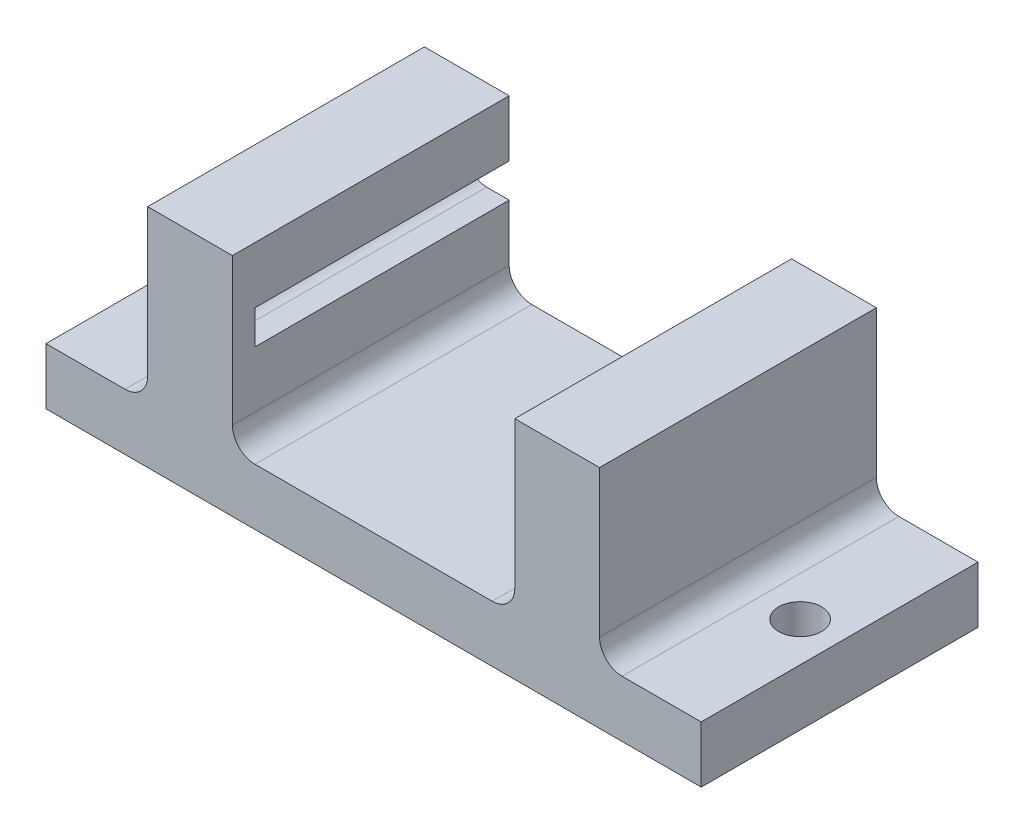
SolidWorks part; units mm, degrees
material "PVC Rigid"
ref_plane "Front Plane" through (0, 0, 0) normal (0, 0, 1) x (1, 0, 0)
ref_plane "Top Plane" through (0, 0, 0) normal (0, 1, 0) x (1, 0, 0)
ref_plane "Right Plane" through (0, 0, 0) normal (1, 0, 0) x (0, 0, -1)
sketch "Sketch2" plane through (0, 0, 0) normal (0, 0, 1) x (1, 0, 0)
  line L0 (13.335, -19.05) -> (0, -19.05)
  line L1 (0, -25.4) -> (36.83, -25.4)
  line L2 (36.83, -25.4) -> (36.83, -19.05)
  line L3 (25.4, 0) -> (15.875, 0)
  line L4 (15.875, 0) -> (15.875, -6.35)
  line L5 (0, -19.05) -> (0, -25.4)
  line L6 (15.875, -16.51) -> (15.875, -10.16)
  line L7 (25.4, -16.51) -> (25.4, 0)
  line L8 (36.83, -19.05) -> (27.94, -19.05)
  line L9 (15.875, -10.16) -> (18.415, -10.16)
  line L10 (15.875, -6.35) -> (18.415, -6.35)
  arc A0 (13.335, -19.05) -> (15.875, -16.51) centre (13.335, -16.51) ccw
  arc A1 (18.415, -10.16) -> (18.415, -6.35) centre (18.415, -8.255) ccw
  arc A2 (25.4, -16.51) -> (27.94, -19.05) centre (27.94, -16.51) ccw
  dimension "D3" = 2.54
  dimension "D5" = 1.905
  dimension "D9" = 2.54
  dimension "D1" = 25.4
  dimension "D2" = 6.35
  dimension "D4" = 15.875
  dimension "D6" = 25.4
  dimension "D7" = 6.35
  dimension "D8" = 6.35
  dimension "D10" = 8.89
  dimension "D11" = 2.54
extrude "Base" add sketch "Sketch2" along normal blind 28.575
sketch "Sketch5" plane through (0, 0, 28.575) normal (0, 0, 1) x (1, 0, 0)
  line L1 (0, -25.4) -> (36.83, -25.4)
  line L2 (0, -19.05) -> (0, -25.4) construction
  line L3 (13.335, -19.05) -> (0, -19.05) construction
  line L4 (36.83, -25.4) -> (36.83, -19.05) construction
  line L6 (36.83, -19.05) -> (27.94, -19.05) construction
  line L7 (25.4, -16.51) -> (25.4, 0) construction
  line L8 (36.83, -25.4) -> (36.83, -19.05)
  line L9 (36.83, -19.05) -> (27.94, -19.05)
  line L10 (25.4, -16.51) -> (25.4, 0)
  line L11 (15.875, -10.16) -> (15.875, -16.51) construction
  line L12 (15.875, 0) -> (15.875, -6.35) construction
  line L13 (25.4, 0) -> (15.875, 0) construction
  line L14 (0, -19.05) -> (0, -25.4)
  line L15 (13.335, -19.05) -> (0, -19.05)
  line L16 (15.875, -10.16) -> (15.875, -16.51)
  line L17 (15.875, 0) -> (15.875, -6.35)
  line L18 (25.4, 0) -> (15.875, 0)
  line L19 (15.875, -6.35) -> (15.875, -10.16)
  arc A0 (25.4, -16.51) -> (27.94, -19.05) centre (27.94, -16.51) ccw construction
  arc A1 (25.4, -16.51) -> (27.94, -19.05) centre (27.94, -16.51) ccw
  arc A2 (13.335, -19.05) -> (15.875, -16.51) centre (13.335, -16.51) ccw construction
  arc A3 (13.335, -19.05) -> (15.875, -16.51) centre (13.335, -16.51) ccw
extrude "Back Plate" add sketch "Sketch5" along normal blind 2.54
sketch "Sketch4" plane through (0, -19.05, 0) normal (0, 1, 0) x (1, 0, 0)
  line L0 (36.83, 0) -> (27.94, 0) construction
  line L1 (36.83, -31.115) -> (36.83, 0) construction
  circle A0 centre (32.385, -15.5575) radius 2.413
  point P4 (32.385, 0)
  point P7 (36.83, -15.5575)
  dimension "D1" = 4.826
extrude "Mounting Holes" cut sketch "Sketch4" against normal through all
mirror "Mirror" about plane through (0, 0, 0) normal (1, 0, 0) of "Back Plate", "Base", "Mounting Holes"
